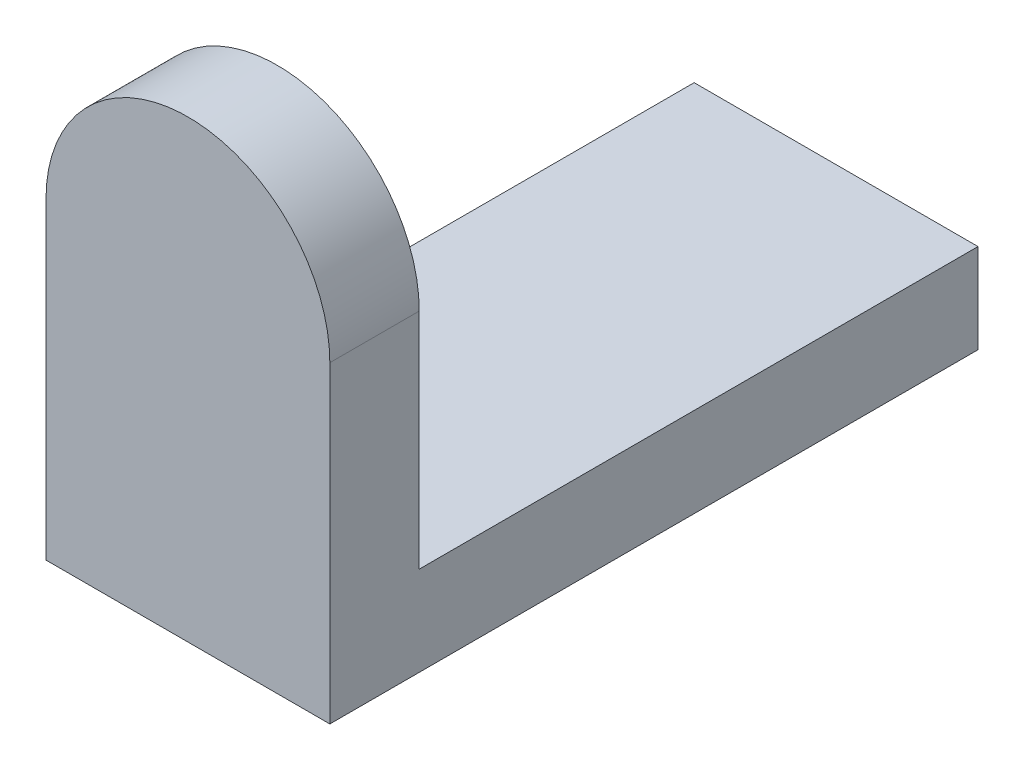
SolidWorks part; units mm, degrees
ref_plane "Front Plane" through (0, 0, 0) normal (0, 0, 1) x (1, 0, 0)
ref_plane "Top Plane" through (0, 0, 0) normal (0, 1, 0) x (1, 0, 0)
ref_plane "Right Plane" through (0, 0, 0) normal (1, 0, 0) x (0, 0, -1)
sketch "Sketch1" plane through (0, 0, 0) normal (0, 1, 0) x (1, 0, 0)
  line L1 (-12.7, -25) -> (12.7, -25)
  line L2 (-12.7, -25) -> (-12.7, 25)
  line L3 (-12.7, 25) -> (12.7, 25)
  line L4 (12.7, -25) -> (12.7, 25)
  line L5 (-12.7, -25) -> (12.7, 25) construction
  line L6 (-12.7, 25) -> (12.7, -25) construction
  point P0 (0, 0)
  dimension "D1" = 25.4
  dimension "D2" = 50
extrude "Boss-Extrude2" add sketch "Sketch1" along normal blind 8
sketch "Sketch4" plane through (0, 0, 25) normal (0, 0, 1) x (1, 0, 0)
  line L0 (12.7, 8) -> (12.7, 0) construction
  line L5 (-12.7, 0) -> (12.7, 0)
  line L6 (-12.7, 0) -> (-12.7, 28)
  line L7 (-12.7, 28) -> (12.7, 28) construction
  line L8 (12.7, 0) -> (12.7, 28)
  line L9 (-12.7, 8) -> (12.7, 8) construction
  arc A0 (12.7, 28) -> (-12.7, 28) centre (0, 28) ccw
  dimension "D1" = 20
extrude "Boss-Extrude4" add sketch "Sketch4" along normal blind 8
